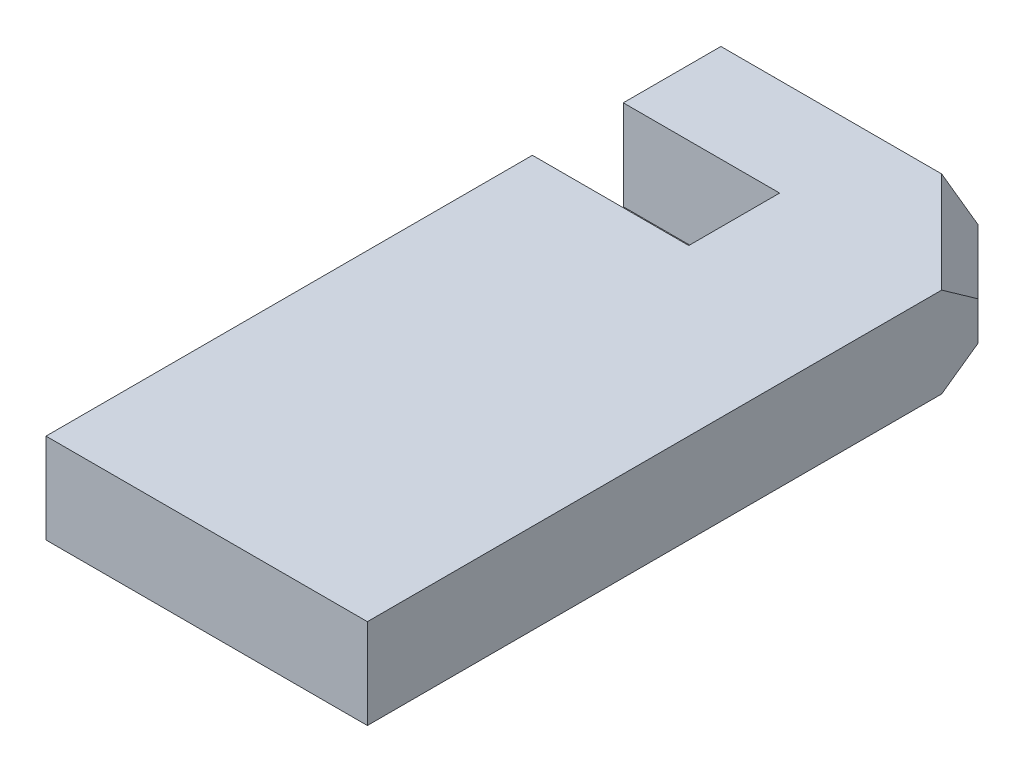
SolidWorks part; units mm, degrees
ref_plane "前视基准面" through (0, 0, 0) normal (0, 0, 1) x (1, 0, 0)
ref_plane "上视基准面" through (0, 0, 0) normal (0, 1, 0) x (1, 0, 0)
ref_plane "右视基准面" through (0, 0, 0) normal (1, 0, 0) x (0, 0, -1)
sketch "草图1" plane through (0, 0, 0) normal (0, 1, 0) x (1, 0, 0)
  line L0 (40, 105) -> (50, 95)
  line L1 (0, 0) -> (50, 0)
  line L2 (0, 0) -> (0, 75.675)
  line L3 (0, 105) -> (40, 105)
  line L4 (50, 0) -> (50, 95)
  line L5 (0, 89.814) -> (0, 105)
  line L6 (0, 89.814) -> (24.3254, 89.814)
  line L8 (0, 75.675) -> (24.3254, 75.675)
  line L9 (24.3254, 89.814) -> (24.3254, 75.675)
  point P1 (50, 105)
  dimension "D1" = 50
  dimension "D2" = 105
extrude "凸台-拉伸1" add sketch "草图1" along normal blind 14
chamfer "倒角1" distance 4 angle 45 2 edges at (45, 0, -100) (45, 14, -100)
